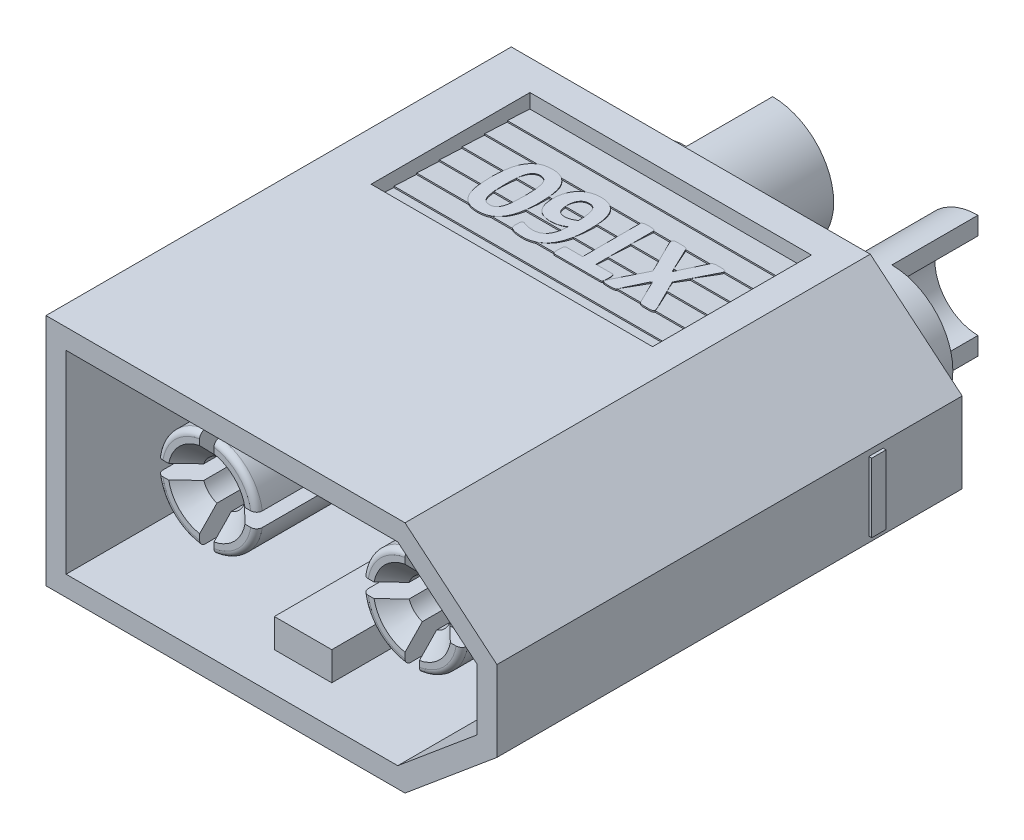
SolidWorks part; units mm, degrees
material "Náilon 101"
ref_plane "Plano frontal" through (0, 0, 0) normal (0, 0, 1) x (1, 0, 0)
ref_plane "Plano superior" through (0, 0, 0) normal (0, 1, 0) x (1, 0, 0)
ref_plane "Plano direito" through (0, 0, 0) normal (1, 0, 0) x (0, 0, -1)
sketch "Esboço1" plane through (0, 0, 0) normal (0, 0, 1) x (1, 0, 0)
  line L0 (0, 0) -> (0, 4.075)
  line L1 (0, 4.075) -> (12.5, 4.075)
  line L2 (12.5, 4.075) -> (15.7, 1.4)
  line L3 (15.7, 1.4) -> (15.7, -1.4)
  line L4 (15.7, 0) -> (0, 0) construction
  line L5 (12.5, -4.075) -> (15.7, -1.4)
  line L6 (0, -4.075) -> (12.5, -4.075)
  line L7 (0, 0) -> (0, -4.075)
  dimension "D1" = 8.15
  dimension "D2" = 12.5
  dimension "D3" = 15.7
  dimension "D4" = 2.8
extrude "Ressalto-extrusão1" add sketch "Esboço1" against normal blind 16.2
sketch "Esboço2" plane through (0, 0, 0) normal (0, 0, 1) x (1, 0, 0)
  line L12 (0.7, 3.375) -> (0.7, -3.375)
  line L13 (0.7, -3.375) -> (12.246, -3.375)
  line L14 (12.246, -3.375) -> (15, -1.0728)
  line L15 (15, -1.0728) -> (15, 1.0728)
  line L16 (15, 1.0728) -> (12.246, 3.375)
  line L17 (12.246, 3.375) -> (0.7, 3.375)
  line L18 (0.7, 3.375) -> (0.7, -3.375)
  line L19 (0.7, -3.375) -> (12.246, -3.375)
  line L20 (12.246, -3.375) -> (15, -1.0728)
  line L21 (15, -1.0728) -> (15, 1.0728)
  line L22 (15, 1.0728) -> (12.246, 3.375)
  line L23 (12.246, 3.375) -> (0.7, 3.375)
  dimension "D1" = 0.7
extrude "Corte-extrusão1" cut sketch "Esboço2" against normal blind 9.3
sketch "Esboço3" plane through (15.7, 0, 0) normal (1, 0, 0) x (0, 0, -1)
  line L0 (13.2, 0) -> (16.2, 0) construction
  line L1 (12.95, -1.2) -> (13.45, -1.2)
  line L2 (12.95, -1.2) -> (12.95, 1.2)
  line L3 (12.95, 1.2) -> (13.45, 1.2)
  line L4 (13.45, -1.2) -> (13.45, 1.2)
  line L5 (12.95, -1.2) -> (13.45, 1.2) construction
  line L6 (12.95, 1.2) -> (13.45, -1.2) construction
  line L7 (16.2, -1.4) -> (16.2, 1.4) construction
  point P0 (13.2, 0)
  dimension "D1" = 0.5
  dimension "D2" = 2.4
  dimension "D3" = 3
extrude "Ressalto-extrusão2" add sketch "Esboço3" along normal blind 0.1 and the other way offset from surface (15.8 mm away) 0.1 other way up to face at (0, 0, -8.1)
sketch "Esboço4" plane through (0, 0, 0) normal (-1, 0, 0) x (0, 0, 1)
  line L0 (-13.45, 0) -> (-12.95, 0) construction
  line L1 (-13.45, -1.2) -> (-13.45, 1.2) construction
  line L2 (-12.95, 1.2) -> (-12.95, -1.2) construction
  line L3 (-12.95, 1.2) -> (-13.45, 1.2) construction
  line L4 (-14.4, -0.25) -> (-12, -0.25)
  line L5 (-14.4, -0.25) -> (-14.4, 0.25)
  line L6 (-14.4, 0.25) -> (-12, 0.25)
  line L7 (-12, -0.25) -> (-12, 0.25)
  line L8 (-14.4, -0.25) -> (-12, 0.25) construction
  line L9 (-14.4, 0.25) -> (-12, -0.25) construction
  point P6 (-13.2, 0)
extrude "Ressalto-extrusão3" add sketch "Esboço4" along normal up to surface (0.1 mm away) up to face at (-0.1, 0, -13.2)
sketch "Esboço5" plane through (0, 0, -16.2) normal (0, 0, -1) x (-1, 0, 0)
  line L0 (-15.7, 0) -> (-11.25, 0) construction
  line L1 (-15.7, -1.4) -> (-15.7, 1.4) construction
  line L2 (-11.25, 0) -> (-4.1, 0) construction
  line L3 (-4.1, 0) -> (0, 0) construction
  line L4 (0, 0.25) -> (0, -0.25) construction
  circle A0 centre (-4.1, 0) radius 2.925
  circle A1 centre (-11.25, 0) radius 2.925
  dimension "D1" = 5.85
  dimension "D2" = 7.15
  dimension "D3" = 4.1
extrude "Corte-extrusão2" cut sketch "Esboço5" against normal blind 3.5
sketch "Esboço6" plane through (0, 0, -12.7) normal (0, 0, -1) x (-1, 0, 0)
  circle A2 centre (-11.25, 0) radius 2.125
  circle A3 centre (-4.1, 0) radius 2.125
  dimension "D1" = 4.25
extrude "Corte-extrusão3" cut sketch "Esboço6" against normal through all
sketch "Esboço7" plane through (0, 0, -16.2) normal (0, 0, -1) x (-1, 0, 0)
  circle A0 centre (-11.25, 0) radius 2.125 construction
  circle A1 centre (-4.1, 0) radius 2.125 construction
  circle A2 centre (-11.25, 0) radius 2.125
  circle A3 centre (-4.1, 0) radius 2.125
extrude "Ressalto-extrusão4" add sketch "Esboço7" along normal blind 5 and the other way offset from surface (7.1 mm away) 0.2 other way up to face at (13.375, 0, -9.3)
hole_wizard "Furo de diâmetro Ø3.0 (3)1" positions "Esboço9" profile "Esboço8" hole size "Ø3.0" standard "Métrico Ansi"
sketch "Esboço9" plane through (0, 0, -21.2) normal (0, 0, -1) x (-1, 0, 0)
  point P0 (-11.25, 0)
  point P1 (-4.1, 0)
sketch "Esboço8" plane through (11.25, 0, -21.2) normal (1, 0, 0) x (0, 1, 0)
  line L0 (0, 0) -> (0, 9.9013)
  line L1 (0, 9.9013) -> (1.5, 9)
  line L2 (1.5, 9) -> (1.5, 0)
  line L5 (1.5, 0) -> (0, 0)
  line L10 (0, 9.9013) -> (-1.5, 9) construction
  line L11 (0, -6.35) -> (0, 107.95) construction
  dimension "Hole Dia." = 3
  dimension "Hole Depth" = 9
  dimension "Drill Angle" = 118
sketch "Esboço10" plane through (0, 4.075, 0) normal (0, 1, 0) x (1, 0, 0)
  line L0 (4.1, 21.2) -> (11.25, 21.2) construction
  line L1 (5.6, 21.2) -> (2.6, 21.2) construction
  line L2 (13.375, 21.2) -> (9.125, 21.2) construction
  line L3 (7.675, 21.2) -> (7.675, 16.2) construction
  line L4 (12.5, 16.2) -> (0, 16.2) construction
  line L5 (1.975, 21.2) -> (1.975, 12.7) construction
  line L6 (4.1, 21.2) -> (1.975, 21.2)
  line L7 (4.1, 21.2) -> (4.1, 18.2)
  line L8 (4.1, 18.2) -> (1.975, 18.2)
  line L9 (1.975, 21.2) -> (1.975, 18.2)
  line L10 (13.375, 21.2) -> (13.375, 18.2)
  line L11 (11.25, 18.2) -> (13.375, 18.2)
  line L12 (11.25, 21.2) -> (11.25, 18.2)
  line L13 (11.25, 21.2) -> (13.375, 21.2)
  dimension "D1" = 3
extrude "Corte-extrusão4" cut sketch "Esboço10" against normal through all
sketch "Esboço11" plane through (0, 0, -9.1) normal (0, 0, 1) x (1, 0, 0)
  line L0 (4.1, 1.75) -> (4.1, -1.75) construction
  line L1 (3.85, 1.7321) -> (3.85, 0.7071)
  line L2 (5.85, 0) -> (2.35, 0) construction
  line L3 (4.35, 1.7321) -> (4.35, 0.7071)
  line L4 (5.8321, 0.25) -> (4.8071, 0.25)
  line L5 (5.8321, -0.25) -> (4.8071, -0.25)
  line L6 (5.85, 0.25) -> (2.35, 0.25) construction
  line L7 (5.85, -0.25) -> (2.35, -0.25) construction
  line L8 (3.85, 1.75) -> (3.85, -1.75) construction
  line L9 (4.35, 1.75) -> (4.35, -1.75) construction
  line L10 (4.1, 0) -> (11.25, 0) construction
  line L11 (7.675, 0) -> (7.675, -4.075) construction
  line L12 (0, -4.075) -> (12.5, -4.075) construction
  line L13 (11.9571, 0.25) -> (12.9821, 0.25)
  line L14 (4.35, -0.7071) -> (4.35, -1.7321)
  line L15 (3.85, -0.7071) -> (3.85, -1.7321)
  line L16 (3.3929, -0.25) -> (2.3679, -0.25)
  line L17 (3.3929, 0.25) -> (2.3679, 0.25)
  line L18 (11.9571, -0.25) -> (12.9821, -0.25)
  line L19 (11.5, -0.7071) -> (11.5, -1.7321)
  line L20 (11, -0.7071) -> (11, -1.7321)
  line L21 (9.5179, -0.25) -> (10.5429, -0.25)
  line L22 (9.5179, 0.25) -> (10.5429, 0.25)
  line L23 (11, 1.7321) -> (11, 0.7071)
  line L24 (11.5, 1.7321) -> (11.5, 0.7071)
  arc A0 (4.35, -1.7321) -> (5.8321, -0.25) centre (4.1, 0) ccw
  arc A1 (3.3929, -0.25) -> (3.85, -0.7071) centre (4.1, 0) ccw
  arc A2 (3.85, 0.7071) -> (3.3929, 0.25) centre (4.1, 0) ccw
  arc A3 (4.8071, 0.25) -> (4.35, 0.7071) centre (4.1, 0) ccw
  arc A4 (4.35, -0.7071) -> (4.8071, -0.25) centre (4.1, 0) ccw
  arc A5 (5.8321, 0.25) -> (4.35, 1.7321) centre (4.1, 0) ccw
  arc A6 (3.85, 1.7321) -> (2.3679, 0.25) centre (4.1, 0) ccw
  arc A7 (2.3679, -0.25) -> (3.85, -1.7321) centre (4.1, 0) ccw
  circle A8 centre (4.1, 0) radius 2.125 construction
  circle A9 centre (11.25, 0) radius 2.125 construction
  arc A10 (12.9821, -0.25) -> (11.5, -1.7321) centre (11.25, 0) cw
  arc A11 (11.5, 1.7321) -> (12.9821, 0.25) centre (11.25, 0) cw
  arc A12 (9.5179, 0.25) -> (11, 1.7321) centre (11.25, 0) cw
  arc A13 (11, -0.7071) -> (10.5429, -0.25) centre (11.25, 0) cw
  arc A14 (10.5429, 0.25) -> (11, 0.7071) centre (11.25, 0) cw
  arc A15 (11.5, 0.7071) -> (11.9571, 0.25) centre (11.25, 0) cw
  arc A16 (11.9571, -0.25) -> (11.5, -0.7071) centre (11.25, 0) cw
  arc A17 (11, -1.7321) -> (9.5179, -0.25) centre (11.25, 0) cw
  dimension "D1" = 3.5
  dimension "D2" = 1.5
  dimension "D3" = 0.25
  dimension "D4" = 0.25
  dimension "D5" = 0.25
  dimension "D6" = 0.25
extrude "Ressalto-extrusão5" add sketch "Esboço11" along normal offset from surface (7.6 mm away) 1.5 up to face at (9.3153, 0, 0)
fillet "Filete1" radius 0.2 8 edges at (10.0126, -1.2374, -1.5) (12.4874, -1.2374, -1.5) (12.4874, 1.2374, -1.5) (10.0126, 1.2374, -1.5) (2.8626, -1.2374, -1.5) (5.3374, -1.2374, -1.5) (5.3374, 1.2374, -1.5) (2.8626, 1.2374, -1.5)
chamfer "Chanfro1" distance 0.6 angle 45 8 edges at (4.6303, -0.5303, -1.5) (3.5697, -0.5303, -1.5) (10.7197, -0.5303, -1.5) (11.7803, -0.5303, -1.5) (11.7803, 0.5303, -1.5) (10.7197, 0.5303, -1.5) (3.5697, 0.5303, -1.5) (4.6303, 0.5303, -1.5)
sketch "Esboço12" plane through (0, 0, 0) normal (-1, 0, 0) x (0, 0, 1)
  line L0 (-15.15, 4.075) -> (-15.15, 3.575)
  line L1 (-16.2, 4.075) -> (0, 4.075) construction
  line L2 (-15.15, 3.575) -> (-14.36, 3.625)
  line L3 (-14.36, 3.625) -> (-14.36, 3.575)
  line L4 (-15.15, 3.575) -> (-9.62, 3.575) construction
  line L5 (-16.2, 4.075) -> (-16.2, -4.075) construction
  line L6 (-14.36, 3.575) -> (-13.57, 3.625)
  line L7 (-13.57, 3.625) -> (-13.57, 3.575)
  line L8 (-13.57, 3.575) -> (-12.78, 3.625)
  line L9 (-12.78, 3.625) -> (-12.78, 3.575)
  line L10 (-12.78, 3.575) -> (-11.99, 3.625)
  line L11 (-11.99, 3.625) -> (-11.99, 3.575)
  line L12 (-11.99, 3.575) -> (-11.2, 3.625)
  line L13 (-11.2, 3.625) -> (-11.2, 3.575)
  line L14 (-11.2, 3.575) -> (-10.41, 3.625)
  line L15 (-10.41, 3.625) -> (-10.41, 3.575)
  line L16 (-10.41, 3.575) -> (-9.62, 3.625)
  line L17 (-9.62, 3.625) -> (-9.62, 3.575) construction
  line L18 (-15.15, 3.575) -> (-14.36, 3.575) construction
  line L19 (-9.62, 3.625) -> (-9.62, 4.075)
  line L20 (-15.15, 4.075) -> (-9.62, 4.075)
  line L21 (-9.62, 4.075) -> (-9.6373, 4.0753)
  line M2 (0, 4.075) -> (-16.2, 4.075)
  dimension "D1" = 0.5
  dimension "D2" = 0.79
  dimension "D3" = 0.05
  dimension "D4" = 1.05
  dimension "D6" = 0.79
  dimension "D5" = 7
extrude "Corte-extrusão5" cut sketch "Esboço12" against normal blind 9.8 from offset 1.7 contours L16 L19 L0 L2 L3 L6 L7 L8 L9 L10 L11 L12 L13 L14 L15 M2 offset against normal yes
mirror "Espelhar1" about plane through (0, 0, 0) normal (0, 1, 0) of "Corte-extrusão5"
ref_plane "Plano1" through (0, 3.575, 0) normal (0, 1, 0) x (-1, 0, 0)
sketch "Esboço13" plane through (0, 3.575, 0) normal (0, 1, 0) x (-1, 0, 0)
  line L0 (-10.1, -13.635) -> (-3.1, -13.635) construction
  line L1 (-3.1, -13.635) -> (-6.6, -13.635) construction
  line L2 (-6.6, -13.635) -> (-6.6, -15.15) construction
  line L4 (-11.5, -15.15) -> (-1.7, -15.15) construction
  line L5 (-10.1, -13.635) -> (-10.1, -11.135) construction
  line L6 (-10.1, -11.135) -> (-3.1, -11.135) construction
  line L7 (-3.1, -11.135) -> (-3.1, -13.635) construction
  line L8 (-6.6, -11.135) -> (-6.6, -9.62) construction
  line L9 (-11.5, -9.62) -> (-1.7, -9.62) construction
  text T0 "XT60" font "Calibri" height 2.5
  dimension "D1" = 7
  dimension "D2" = 2.5
extrude "Ressalto-extrusão6" add sketch "Esboço13" along normal up to vertex (0.05 mm away) up to point (11.5, 3.625, -11.2)
ref_plane "Plano2" through (0, -3.575, 0) normal (0, 1, 0) x (-1, 0, 0)
sketch "Esboço14" plane through (0, -3.575, 0) normal (0, 1, 0) x (-1, 0, 0)
  line L0 (-6.6, -9.62) -> (-6.6, -10.735) construction
  line L1 (-11.5, -9.62) -> (-1.7, -9.62) construction
  line L2 (-6.6, -10.735) -> (-2.8, -10.735) construction
  line L3 (-2.8, -10.735) -> (-2.8, -14.035) construction
  line L4 (-2.8, -14.035) -> (-10.4, -14.035) construction
  line L5 (-10.4, -14.035) -> (-10.4, -10.735) construction
  line L6 (-10.4, -10.735) -> (-6.6, -10.735) construction
  line L7 (-6.6, -14.035) -> (-6.6, -15.15) construction
  line L8 (-11.5, -15.15) -> (-1.7, -15.15) construction
  text T0 "TGY" font "Calibri" height 3.3
  dimension "D1" = 3.3
  dimension "D2" = 7.6
extrude "Ressalto-extrusão7" add sketch "Esboço14" against normal up to vertex (0.05 mm away) up to point (1.7, -3.625, -10.41)
sketch "Esboço15" plane through (0, 0, -9.3) normal (0, 0, 1) x (1, 0, 0)
  line L0 (0.7, -3.375) -> (12.246, -3.375) construction
  line L1 (6.6, -3.375) -> (8.6, -3.375)
  line L2 (6.6, -3.375) -> (6.6, -2.375)
  line L3 (6.6, -2.375) -> (8.6, -2.375)
  line L4 (8.6, -3.375) -> (8.6, -2.375)
  line L5 (0.7, 3.375) -> (0.7, -3.375) construction
  dimension "D1" = 5.9
  dimension "D2" = 1
  dimension "D3" = 2
extrude "Ressalto-extrusão8" add sketch "Esboço15" along normal offset from surface (7.95 mm away) 1.35 up to face at (9.3153, 0, 0)
sketch "Esboço16" plane through (0, 0, -9.3) normal (0, 0, 1) x (1, 0, 0)
  line L0 (7.6, -0.125) -> (7.6, -2.375) construction
  line L1 (7.05, -2.175) -> (8.15, -2.175)
  line L2 (7.05, -2.175) -> (7.05, 1.925)
  line L3 (7.05, 1.925) -> (8.15, 1.925)
  line L4 (8.15, -2.175) -> (8.15, 1.925)
  line L5 (7.05, -2.175) -> (8.15, 1.925) construction
  line L6 (7.05, 1.925) -> (8.15, -2.175) construction
  line L7 (8.6, -2.375) -> (6.6, -2.375) construction
  point P0 (7.6, -0.125)
  dimension "D1" = 1.1
  dimension "D2" = 4.1
  dimension "D3" = 0.2
extrude "Corte-extrusão6" cut sketch "Esboço16" against normal blind 1
